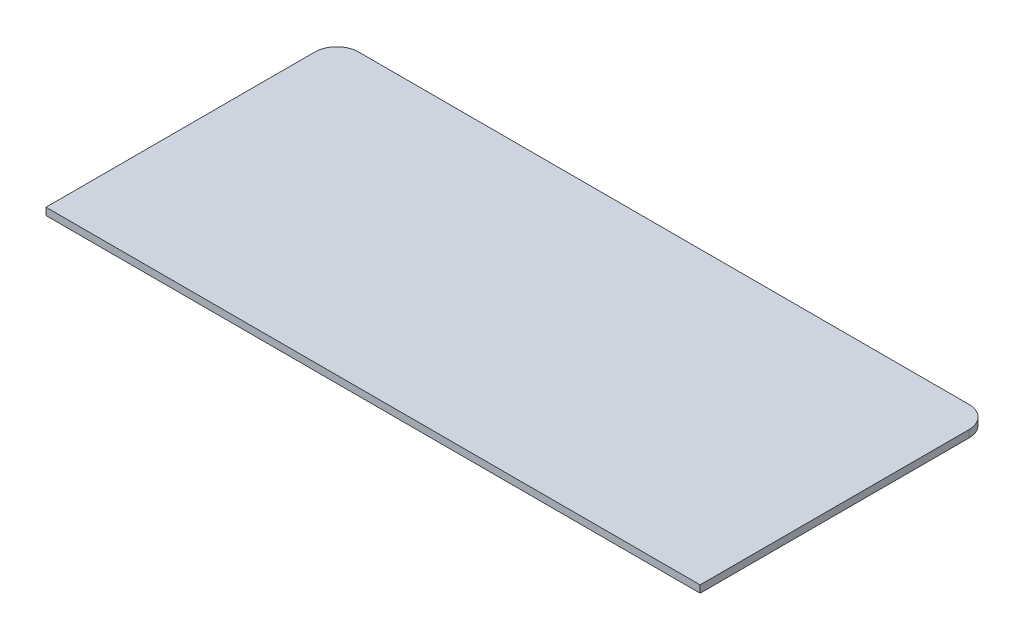
SolidWorks part; units mm, degrees
ref_plane "Front Plane" through (0, 0, 0) normal (0, 0, 1) x (1, 0, 0)
ref_plane "Top Plane" through (0, 0, 0) normal (0, 1, 0) x (1, 0, 0)
ref_plane "Right Plane" through (0, 0, 0) normal (1, 0, 0) x (0, 0, -1)
sketch "Sketch1" plane through (0, 0, 0) normal (0, 1, 0) x (1, 0, 0)
  line L0 (0, 0) -> (4.5, 0)
  line L1 (4.5, 0) -> (4.5, 3.7)
  line L2 (4.2, 4) -> (-4.2, 4)
  line L3 (-4.5, 3.7) -> (-4.5, 0)
  line L4 (-4.5, 0) -> (0, 0)
  arc A0 (4.5, 3.7) -> (4.2, 4) centre (4.2, 3.7) ccw
  arc A1 (-4.2, 4) -> (-4.5, 3.7) centre (-4.2, 3.7) ccw
  point P8 (4.5, 4)
  point P11 (-4.5, 4)
  dimension "D3" = 0.3
  dimension "D1" = 4
  dimension "D2" = 9
extrude "Boss-Extrude1" add sketch "Sketch1" along normal blind 0.1
